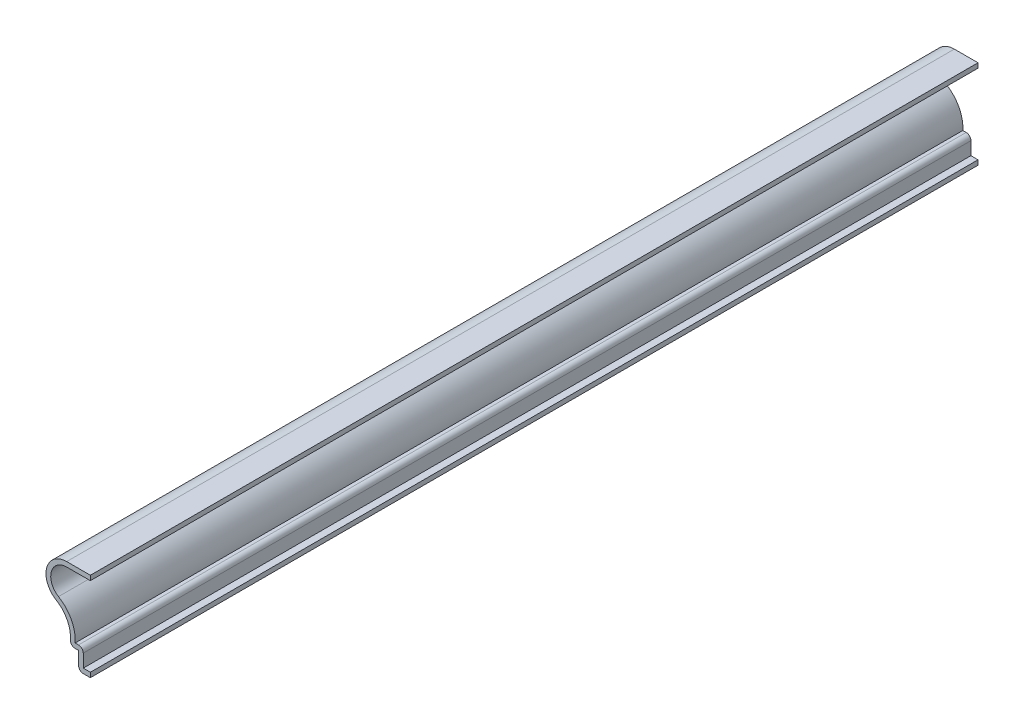
SolidWorks part; units mm, degrees
ref_plane "Front Plane" through (0, 0, 0) normal (0, 0, 1) x (1, 0, 0)
ref_plane "Top Plane" through (0, 0, 0) normal (0, 1, 0) x (1, 0, 0)
ref_plane "Right Plane" through (0, 0, 0) normal (1, 0, 0) x (0, 0, -1)
sketch "Sketch1" plane through (0, 0, 0) normal (0, 0, 1) x (1, 0, 0)
  line L0 (0, 0) -> (-3.175, 0)
  line L1 (-3.175, 0) -> (-3.175, 4.7625)
  line L2 (-3.175, 4.7625) -> (-5.5563, 4.7625)
  line L3 (-6.35, 23.8125) -> (0, 23.8125)
  arc A0 (-5.5563, 4.7625) -> (-9.1961, 13.4843) centre (-13.2619, 6.6671) ccw
  arc A1 (-9.1961, 13.4843) -> (-6.35, 23.8125) centre (-6.35, 18.2563) cw
  point P9 (-13.4937, 4.7625)
  point P11 (-13.4496, 5.5989)
  point P12 (0, 0)
  dimension "D3" = 5.5562
  dimension "D4" = 7.9375
  dimension "D5" = 11.9062
  dimension "D1" = 3.175
  dimension "D2" = 2.3813
  dimension "D6" = 23.8125
  dimension "D7" = 4.7625
extrude "Extrude-Thin1" add sketch "Sketch1" against normal blind 238.125 thin
fillet "Fillet1" radius 1.27 3 edges at (-3.175, 0, -119.0625) (-1.905, 6.0325, -119.0625) (-5.5563, 4.7625, -119.0625)
